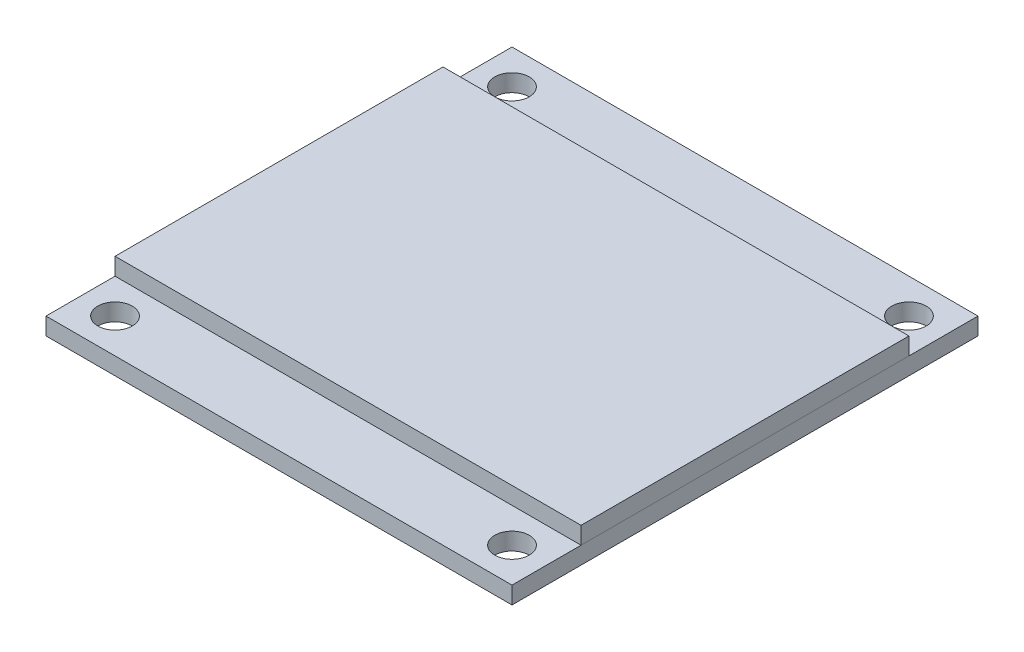
SolidWorks part; units mm, degrees
ref_plane "Front Plane" through (0, 0, 0) normal (0, 0, 1) x (1, 0, 0)
ref_plane "Top Plane" through (0, 0, 0) normal (0, 1, 0) x (1, 0, 0)
ref_plane "Right Plane" through (0, 0, 0) normal (1, 0, 0) x (0, 0, -1)
sketch "Sketch1" plane through (0, 0, 0) normal (0, 1, 0) x (1, 0, 0)
  line L1 (-13.5, 13.5) -> (13.5, 13.5)
  line L2 (-13.5, 13.5) -> (-13.5, -13.5)
  line L3 (-13.5, -13.5) -> (13.5, -13.5)
  line L4 (13.5, 13.5) -> (13.5, -13.5)
  line L5 (-13.5, 13.5) -> (13.5, -13.5) construction
  line L6 (-13.5, -13.5) -> (13.5, 13.5) construction
  circle A0 centre (-11.5, 11.5) radius 1
  circle A1 centre (11.5, 11.5) radius 1
  circle A2 centre (11.5, -11.5) radius 1
  circle A3 centre (-11.5, -11.5) radius 1
  point P0 (0, 0)
  point P14 (0, 0)
  point P15 (0, 0)
  point P16 (0, 0)
  point P17 (0, 0)
  dimension "D2" = 2
  dimension "D5" = 2
  dimension "D1" = 27
  dimension "D3" = 2
  dimension "D4" = 2
  dimension "D6" = 2
extrude "Boss-Extrude1" add sketch "Sketch1" along normal blind 1
sketch "Sketch2" plane through (0, 1, 0) normal (0, 1, 0) x (1, 0, 0)
  line L0 (13.5, -13.5) -> (13.5, 13.5) construction
  line L1 (-13.5, 9.5) -> (13.5, 9.5)
  line L2 (-13.5, 9.5) -> (-13.5, -9.5)
  line L3 (-13.5, -9.5) -> (13.5, -9.5)
  line L4 (13.5, 9.5) -> (13.5, -9.5)
  line L5 (-13.5, 9.5) -> (13.5, -9.5) construction
  line L6 (-13.5, -9.5) -> (13.5, 9.5) construction
  point P0 (0, 0)
  dimension "D1" = 19
extrude "Boss-Extrude2" add sketch "Sketch2" along normal blind 1 separate body
